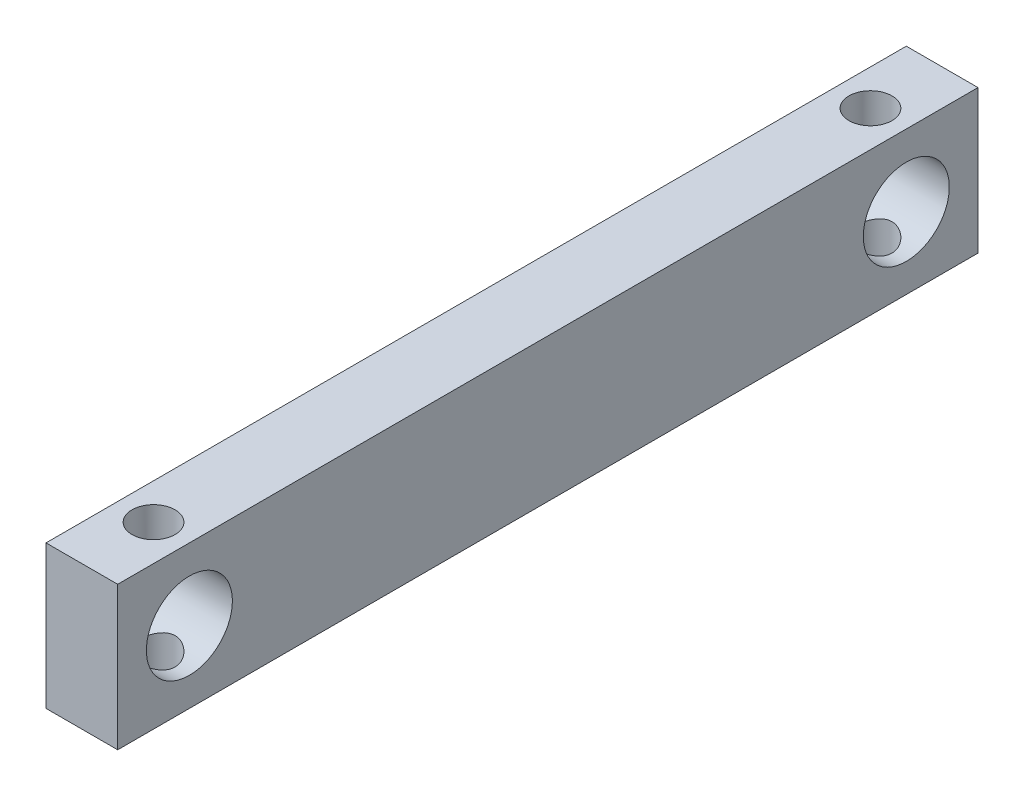
SolidWorks part; units mm, degrees
ref_plane "前基準面" through (0, 0, 0) normal (0, 0, 1) x (1, 0, 0)
ref_plane "上基準面" through (0, 0, 0) normal (0, 1, 0) x (1, 0, 0)
ref_plane "右基準面" through (0, 0, 0) normal (1, 0, 0) x (0, 0, -1)
sketch "草圖1" plane through (0, 0, 0) normal (1, 0, 0) x (0, 0, -1)
  line L0 (0, 7.5824) -> (0, -9.1209) construction
  line L1 (-30, -5) -> (30, -5)
  line L2 (-30, -5) -> (-30, 5)
  line L3 (-30, 5) -> (30, 5)
  line L4 (30, -5) -> (30, 5)
  line L5 (-30, -5) -> (30, 5) construction
  line L6 (-30, 5) -> (30, -5) construction
  circle A0 centre (-25, 0) radius 3
  circle A1 centre (25, 0) radius 3
  point P0 (0, 0)
  dimension "D2" = 6
  dimension "D3" = 5
  dimension "D4" = 50
  dimension "D1" = 10
extrude "填料-伸長1" add sketch "草圖1" along normal mid plane 5
sketch "草圖3" plane through (0, 0, 0) normal (0, 1, 0) x (1, 0, 0)
  line L0 (-9.8365, 0) -> (13.8019, 0) construction
  circle A0 centre (0, 25) radius 1.5
  circle A1 centre (0, -25) radius 1.5
  point P7 (0, 0)
  dimension "D1" = 50
  dimension "D2" = 3
extrude "除料-伸長1" cut sketch "草圖3" against normal through all both and the other way through all
